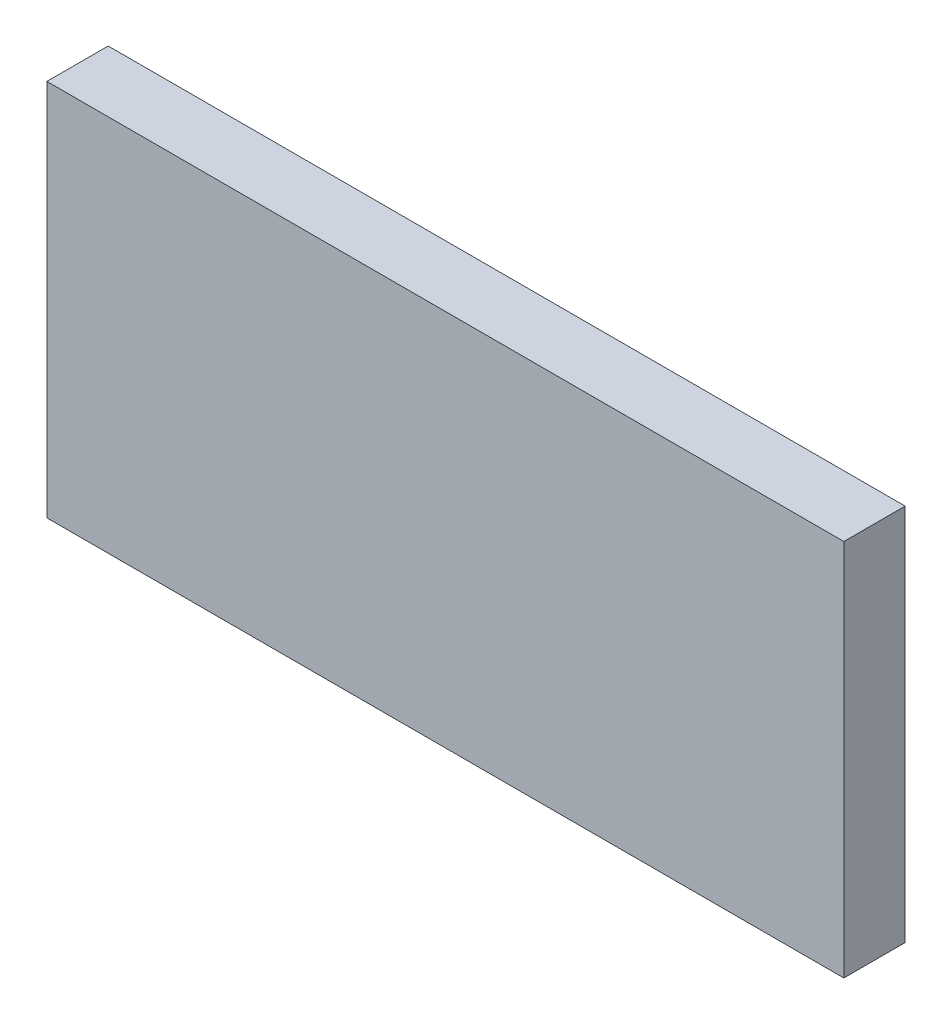
SolidWorks part; units mm, degrees
ref_plane "Front Plane" through (0, 0, 0) normal (0, 0, 1) x (1, 0, 0)
ref_plane "Top Plane" through (0, 0, 0) normal (0, 1, 0) x (1, 0, 0)
ref_plane "Right Plane" through (0, 0, 0) normal (1, 0, 0) x (0, 0, -1)
sketch "Sketch1" plane through (0, 0, 0) normal (0, 0, 1) x (1, 0, 0)
  line L1 (0, 0) -> (39, 0)
  line L2 (0, 0) -> (0, 18.5)
  line L3 (0, 18.5) -> (39, 18.5)
  line L4 (39, 0) -> (39, 18.5)
  dimension "D1" = 39
  dimension "D2" = 18.5
extrude "Boss-Extrude1" add sketch "Sketch1" along normal blind 3
